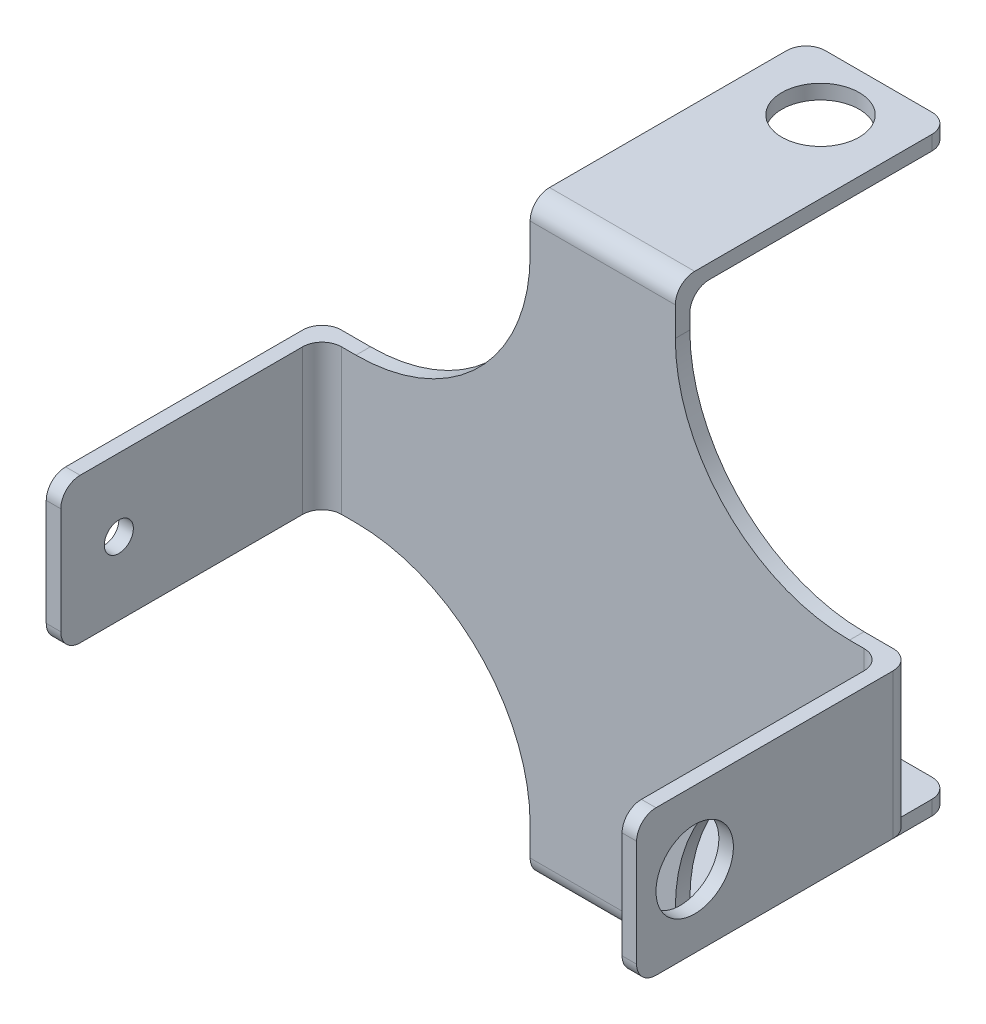
SolidWorks part; units mm, degrees
ref_plane "Front Plane" through (0, 0, 0) normal (0, 0, 1) x (1, 0, 0)
ref_plane "Top Plane" through (0, 0, 0) normal (0, 1, 0) x (1, 0, 0)
ref_plane "Right Plane" through (0, 0, 0) normal (1, 0, 0) x (0, 0, -1)
sketch "Sketch1" plane through (0, 0, 0) normal (0, 0, 1) x (1, 0, 0)
  line L1 (-29, -7.5) -> (29, -7.5)
  line L2 (-29, -7.5) -> (-29, 7.5)
  line L3 (-29, 7.5) -> (29, 7.5)
  line L4 (29, -7.5) -> (29, 7.5)
  line L5 (-29, -7.5) -> (29, 7.5) construction
  line L6 (-29, 7.5) -> (29, -7.5) construction
  line L9 (0, 7.5) -> (0, -7.5) construction
  line L10 (-29, 0) -> (29, 0) construction
  line L15 (-7.5, -29) -> (7.5, -29)
  line L16 (-7.5, -29) -> (-7.5, 29)
  line L17 (-7.5, 29) -> (7.5, 29)
  line L18 (7.5, -29) -> (7.5, 29)
  line L19 (-7.5, -29) -> (7.5, 29) construction
  line L20 (-7.5, 29) -> (7.5, -29) construction
  line L21 (-7.5, 29) -> (7.5, 29)
  point P0 (0, 0)
  point P18 (0, 0)
  dimension "D1" = 15
  dimension "D2" = 58
extrude "Boss-Extrude1" add sketch "Sketch1" along normal blind 1.5 contours L3 L18 L17 L16 | L1 L16 L3 L2 | L1 L18 L3 L16 | L18 L1 L4 L3 | L15 L18 L1 L16
sketch "Sketch2" plane through (0, 0, 1.5) normal (0, 0, 1) x (1, 0, 0)
  line L0 (0, 29) -> (0, -29) construction
  line L1 (-29, 7.5) -> (-30.5, 7.5)
  line L2 (-29, 7.5) -> (-29, -7.5)
  line L3 (-29, -7.5) -> (-30.5, -7.5)
  line L4 (-30.5, 7.5) -> (-30.5, -7.5)
  line L5 (30.5, 7.5) -> (30.5, -7.5)
  line L6 (29, -7.5) -> (30.5, -7.5)
  line L7 (29, 7.5) -> (29, -7.5)
  line L8 (29, 7.5) -> (30.5, 7.5)
  line L9 (-7.5, 29) -> (7.5, 29) construction
  line L10 (29, 0) -> (-29, 0) construction
  line L11 (29, -7.5) -> (29, 7.5) construction
  line L12 (-29, -7.5) -> (-7.5, -7.5) construction
  dimension "D1" = 1.5
extrude "Boss-Extrude2" add sketch "Sketch2" along normal blind 28.5 from offset 1.5 offset against normal yes
sketch "Sketch3" plane through (0, 0, 0) normal (0, 0, -1) x (-1, 0, 0)
  line L1 (7.5, 29) -> (-7.5, 29)
  line L2 (7.5, 29) -> (7.5, 30.5)
  line L3 (7.5, 30.5) -> (-7.5, 30.5)
  line L4 (-7.5, 29) -> (-7.5, 30.5)
  line L5 (7.5, -29) -> (-7.5, -29)
  line L6 (7.5, -29) -> (7.5, -30.5)
  line L7 (7.5, -30.5) -> (-7.5, -30.5)
  line L8 (-7.5, -29) -> (-7.5, -30.5)
  dimension "D1" = 1.5
  dimension "D2" = 1.5
extrude "Boss-Extrude3" add sketch "Sketch3" along normal blind 28.5 from offset 1.5 offset against normal yes
sketch "Sketch4" plane through (30.5, 0, 0) normal (1, 0, 0) x (0, 0, -1)
  line L0 (-28.5, -7.5) -> (-28.5, 7.5) construction
  circle A0 centre (-22.5, 0) radius 1.5
  dimension "D1" = 3
  dimension "D2" = 6
extrude "Cut-Extrude1" cut sketch "Sketch4" against normal through all
sketch "Sketch5" plane through (0, 30.5, 0) normal (0, 1, 0) x (1, 0, 0)
  line L0 (-7.5, 27) -> (7.5, 27) construction
  circle A0 centre (0, 21) radius 1.5
  dimension "D1" = 3
  dimension "D2" = 6
extrude "Cut-Extrude2" cut sketch "Sketch5" against normal through all
fillet "Fillet1" radius 2 8 edges at (-7.5, -29.75, -27) (7.5, -29.75, -27) (-7.5, 29.75, -27) (7.5, 29.75, -27) (-29.75, 7.5, 28.5) (-29.75, -7.5, 28.5) (29.75, -7.5, 28.5) (29.75, 7.5, 28.5)
fillet "Fillet2" radius 2 8 edges at (30.5, 0, 0) (-30.5, 0, 0) (0, -30.5, 1.5) (0, 30.5, 1.5)
fillet "Fillet3" radius 18 4 edges at (-7.5, 7.5, 0.75) (-7.5, -7.5, 0.75) (7.5, -7.5, 0.75) (7.5, 7.5, 0.75)
sketch "Sketch6" plane through (30.5, 0, 0) normal (1, 0, 0) x (0, 0, -1)
  circle A0 centre (-22.5, 0) radius 4
  dimension "D1" = 8
extrude "Cut-Extrude3" cut sketch "Sketch6" against normal up to next
sketch "Sketch7" plane through (0, 30.5, 0) normal (0, 1, 0) x (1, 0, 0)
  circle A0 centre (0, 21) radius 4
  dimension "D1" = 8
extrude "Cut-Extrude4" cut sketch "Sketch7" against normal up to next
